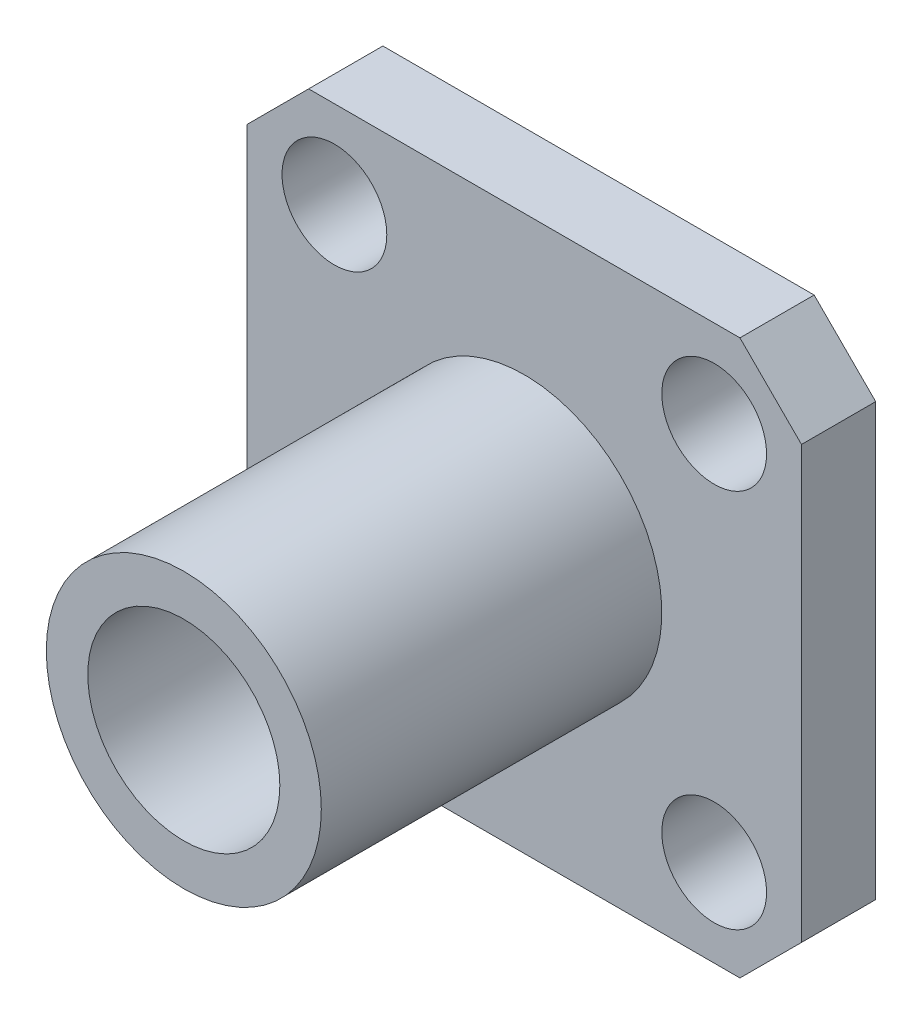
SolidWorks part; units mm, degrees
ref_plane "Front Plane" through (0, 0, 0) normal (1, 0, 0) x (0, 1, 0)
ref_plane "Top Plane" through (0, 0, 0) normal (0, 0, 1) x (0, 1, 0)
ref_plane "Right Plane" through (0, 0, 0) normal (0, 1, 0) x (-1, 0, 0)
sketch "Sketch1" plane through (0, 0, 0) normal (0, 0, 1) x (0, 1, 0)
  line L1 (-6.35, -6.35) -> (6.35, -6.35)
  line L2 (-6.35, -6.35) -> (-6.35, 6.35)
  line L3 (-6.35, 6.35) -> (6.35, 6.35)
  line L4 (6.35, -6.35) -> (6.35, 6.35)
  line L5 (-6.35, -6.35) -> (6.35, 6.35) construction
  line L6 (-6.35, 6.35) -> (6.35, -6.35) construction
  point P0 (0, 0)
  dimension "D1" = 12.7
  dimension "D2" = 12.7
extrude "Boss-Extrude1" add sketch "Sketch1" along normal blind 1.7
chamfer "Chamfer3" distance 1.41 4 edges at (-6.35, 6.35, 0.85) (6.35, 6.35, 0.85) (6.35, -6.35, 0.85) (-6.35, -6.35, 0.85)
sketch "Sketch2" plane through (0, 0, 1.7) normal (0, 0, 1) x (1, 0, 0)
  line L0 (4.94, 6.35) -> (-4.94, 6.35) construction
  line L1 (-6.35, 4.94) -> (-6.35, -4.94) construction
  line L2 (-4.94, -6.35) -> (4.94, -6.35) construction
  line L3 (6.35, -4.94) -> (6.35, 4.94) construction
  circle A0 centre (-4.35, 4.35) radius 1.2
  circle A1 centre (-4.35, -4.35) radius 1.2
  circle A2 centre (4.35, -4.35) radius 1.2
  circle A3 centre (4.35, 4.35) radius 1.2
  dimension "D1" = 2.4
  dimension "D2" = 2
  dimension "D3" = 2
  dimension "D4" = 2.4
  dimension "D5" = 2.4
  dimension "D6" = 2.4
  dimension "D8" = 2
  dimension "D9" = 2
  dimension "D10" = 2
  dimension "D11" = 2
  dimension "D12" = 2
  dimension "D7" = 2
extrude "Cut-Extrude2" cut sketch "Sketch2" against normal through all contours A3 | A2 | A1 | A0
sketch "Sketch3" plane through (0, 0, 1.7) normal (0, 0, 1) x (1, 0, 0)
  circle A0 centre (0, 0) radius 3.15
  circle A1 centre (0, 0) radius 2.2
  dimension "D1" = 6.3
  dimension "D2" = 4.4
extrude "Boss-Extrude2" add sketch "Sketch3" along normal blind 7.8 contours A1 | A0
sketch "Sketch4" plane through (0, 0, 0) normal (0, 0, -1) x (1, 0, 0)
  circle A0 centre (0, 0) radius 0.64
  dimension "D1" = 1.28
extrude "Boss-Extrude3" add sketch "Sketch4" along normal blind 5
